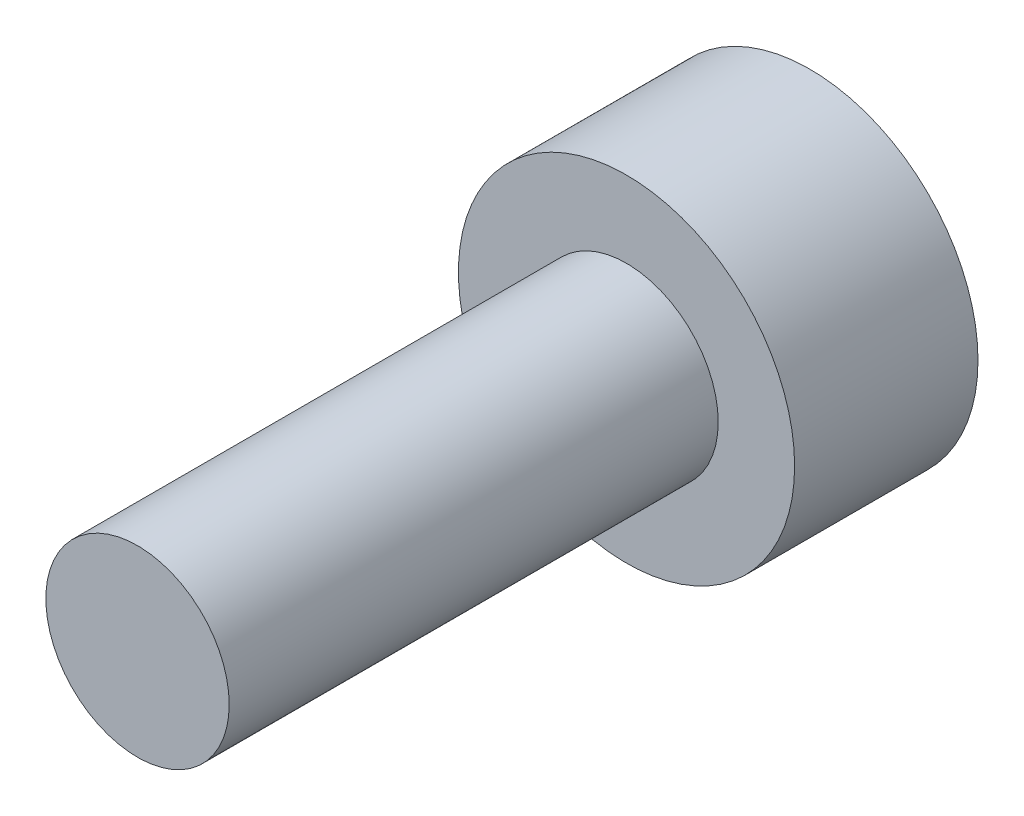
SolidWorks part; units mm, degrees
ref_plane "前视基准面" through (0, 0, 0) normal (0, 0, 1) x (1, 0, 0)
ref_plane "上视基准面" through (0, 0, 0) normal (0, 1, 0) x (1, 0, 0)
ref_plane "右视基准面" through (0, 0, 0) normal (1, 0, 0) x (0, 0, -1)
sketch "草图1" plane through (0, 0, 0) normal (0, 0, 1) x (1, 0, 0)
  circle A0 centre (0, 0) radius 2.75
  dimension "D1" = 5.5
extrude "凸台-拉伸1" add sketch "草图1" along normal blind 3
sketch "草图2" plane through (0, 0, 0) normal (0, 0, -1) x (-1, 0, 0)
  line L1 (0, -1.4434) -> (1.25, -0.7217)
  line L2 (1.25, -0.7217) -> (1.25, 0.7217)
  line L3 (1.25, 0.7217) -> (0, 1.4434)
  line L4 (0, 1.4434) -> (-1.25, 0.7217)
  line L5 (-1.25, 0.7217) -> (-1.25, -0.7217)
  line L6 (-1.25, -0.7217) -> (0, -1.4434)
  circle A0 centre (0, 0) radius 1.25 construction
  circle A1 centre (0, 0) radius 2.75
  circle A2 centre (0, 0) radius 2.75
  dimension "D2" = 2.5
  dimension "D1" = 0
extrude "切除-拉伸1" cut sketch "草图2" against normal blind 1.3 contours L5 L6 L1 L2 L3 L4
sketch "草图3" plane through (0, 0, 3) normal (0, 0, 1) x (1, 0, 0)
  circle A0 centre (0, 0) radius 1.5
  circle A1 centre (0, 0) radius 2.75
  circle A2 centre (0, 0) radius 2.75
  dimension "D2" = 3
  dimension "D1" = 0
extrude "凸台-拉伸2" add sketch "草图3" along normal blind 8 contours A0
